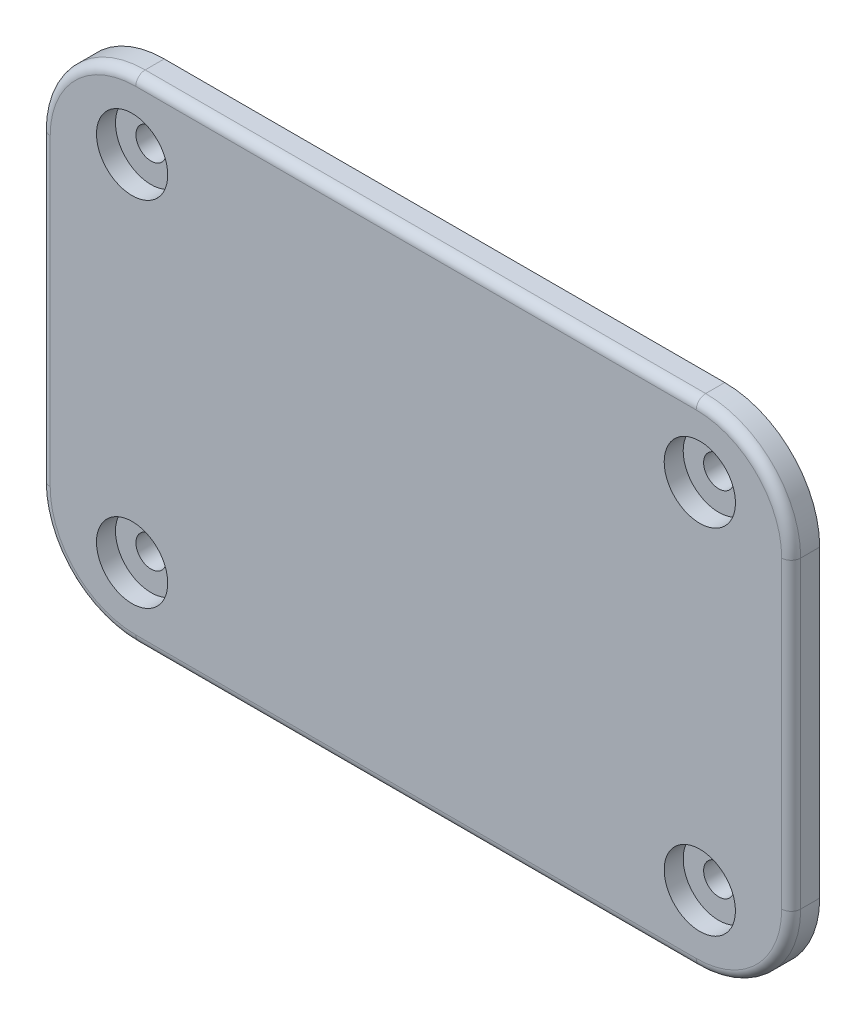
SolidWorks part; units mm, degrees
ref_plane "Ön Düzlem" through (0, 0, 0) normal (0, 0, 1) x (1, 0, 0)
ref_plane "Üst Düzlem" through (0, 0, 0) normal (0, 1, 0) x (1, 0, 0)
ref_plane "Sağ Düzlem" through (0, 0, 0) normal (1, 0, 0) x (0, 0, -1)
sketch "Çizim1" plane through (0, 0, 0) normal (0, 0, 1) x (1, 0, 0)
  line L1 (-29.5, -26) -> (29.5, -26)
  line L2 (-39.5, -16) -> (-39.5, 16)
  line L3 (-29.5, 26) -> (29.5, 26)
  line L4 (39.5, -16) -> (39.5, 16)
  line L5 (-39.5, -26) -> (39.5, 26) construction
  line L6 (-39.5, 26) -> (39.5, -26) construction
  arc A0 (29.5, -26) -> (39.5, -16) centre (29.5, -16) ccw
  arc A1 (-39.5, 16) -> (-29.5, 26) centre (-29.5, 16) cw
  arc A2 (-29.5, -26) -> (-39.5, -16) centre (-29.5, -16) cw
  arc A3 (29.5, 26) -> (39.5, 16) centre (29.5, 16) cw
  point P0 (0, 0)
  dimension "D3" = 10
  dimension "D1" = 79
  dimension "D2" = 52
extrude "Yükseklik-Ekstrüzyon1" add sketch "Çizim1" along normal blind 3
sketch "Çizim4" plane through (0, 0, 0) normal (0, 0, -1) x (-1, 0, 0)
  line L36 (-35.35, 16) -> (-35.35, -16)
  line L37 (29.5, 21.85) -> (-29.5, 21.85)
  line L38 (35.35, -16) -> (35.35, 16)
  line L39 (-29.5, -21.85) -> (29.5, -21.85)
  line L40 (-35.35, 16) -> (-35.35, -16)
  line L41 (29.5, 21.85) -> (-29.5, 21.85)
  line L42 (35.35, -16) -> (35.35, 16)
  line L43 (-29.5, -21.85) -> (29.5, -21.85)
  arc A41 (-35.35, -16) -> (-29.5, -21.85) centre (-29.5, -16) ccw
  arc A42 (-29.5, 21.85) -> (-35.35, 16) centre (-29.5, 16) ccw
  arc A43 (35.35, 16) -> (29.5, 21.85) centre (29.5, 16) ccw
  arc A44 (29.5, -21.85) -> (35.35, -16) centre (29.5, -16) ccw
  arc A45 (-35.35, -16) -> (-29.5, -21.85) centre (-29.5, -16) ccw
  arc A46 (-29.5, 21.85) -> (-35.35, 16) centre (-29.5, 16) ccw
  arc A47 (35.35, 16) -> (29.5, 21.85) centre (29.5, 16) ccw
  arc A48 (29.5, -21.85) -> (35.35, -16) centre (29.5, -16) ccw
  dimension "D1" = 4.15
extrude "Yükseklik-Ekstrüzyon2" add sketch "Çizim4" along normal blind 1.5
fillet "Radyus1" radius 1 8 edges at (0, -26, 3) (-36.5711, -23.0711, 3) (-39.5, 0, 3) (-36.5711, 23.0711, 3) (0, 26, 3) (36.5711, 23.0711, 3) (39.5, 0, 3) (36.5711, -23.0711, 3)
sketch "Çizim5" plane through (0, 0, 3) normal (0, 0, 1) x (1, 0, 0)
  line L0 (30.6791, -15.9455) -> (29.0796, -21.2522) construction
  line L1 (27.1815, -19.2329) -> (32.5771, -17.9648) construction
  line L2 (0, 4.9002) -> (0, -5.0322) construction
  line L3 (21.4256, 0) -> (-21.56, 0) construction
  line L4 (-29.0796, -21.2522) -> (-31.7773, -20.6181) construction
  line L5 (-27.1815, -19.2329) -> (-29.0796, -21.2522) construction
  line L6 (-27.9813, -16.5795) -> (-27.1815, -19.2329) construction
  line L25 (31.7773, -20.6181) -> (32.5771, -17.9648) construction
  line L26 (32.5771, -17.9648) -> (30.6791, -15.9455) construction
  line L27 (30.6791, -15.9455) -> (27.9813, -16.5795) construction
  line L28 (27.9813, -16.5795) -> (27.1815, -19.2329) construction
  line L29 (27.1815, -19.2329) -> (29.0796, -21.2522) construction
  line L30 (29.0796, -21.2522) -> (31.7773, -20.6181) construction
  line L55 (-30.6791, -15.9455) -> (-27.9813, -16.5795) construction
  line L56 (-32.5771, -17.9648) -> (-30.6791, -15.9455) construction
  line L57 (-31.7773, -20.6181) -> (-32.5771, -17.9648) construction
  line L58 (-27.1815, -19.2329) -> (-32.5771, -17.9648) construction
  line L59 (-30.6791, -15.9455) -> (-29.0796, -21.2522) construction
  line L60 (-30.6791, 15.9455) -> (-29.0796, 21.2522) construction
  line L61 (-27.1815, 19.2329) -> (-32.5771, 17.9648) construction
  line L62 (-31.7773, 20.6181) -> (-32.5771, 17.9648) construction
  line L63 (-32.5771, 17.9648) -> (-30.6791, 15.9455) construction
  line L64 (-30.6791, 15.9455) -> (-27.9813, 16.5795) construction
  line L65 (29.0796, 21.2522) -> (31.7773, 20.6181) construction
  line L66 (27.1815, 19.2329) -> (29.0796, 21.2522) construction
  line L67 (27.9813, 16.5795) -> (27.1815, 19.2329) construction
  line L68 (30.6791, 15.9455) -> (27.9813, 16.5795) construction
  line L69 (32.5771, 17.9648) -> (30.6791, 15.9455) construction
  line L70 (31.7773, 20.6181) -> (32.5771, 17.9648) construction
  line L71 (-27.9813, 16.5795) -> (-27.1815, 19.2329) construction
  line L72 (-27.1815, 19.2329) -> (-29.0796, 21.2522) construction
  line L73 (-29.0796, 21.2522) -> (-31.7773, 20.6181) construction
  line L74 (27.1815, 19.2329) -> (32.5771, 17.9648) construction
  line L75 (30.6791, 15.9455) -> (29.0796, 21.2522) construction
  circle A0 centre (29.8793, -18.5988) radius 1.6
  circle A1 centre (-29.8793, -18.5988) radius 1.6
  circle A2 centre (-29.8793, 18.5988) radius 1.6
  circle A3 centre (29.8793, 18.5988) radius 1.6
extrude "Kes-Ekstrüzyon1" cut sketch "Çizim5" against normal blind 5
sketch "Çizim6" plane through (0, 0, 3) normal (0, 0, 1) x (1, 0, 0)
  line L0 (-16.7251, 0) -> (15.2915, 0) construction
  line L1 (0, -7.9643) -> (0, 9.7961) construction
  circle A4 centre (29.8793, -18.5988) radius 3.75
  circle A5 centre (-29.8793, -18.5988) radius 3.75
  circle A6 centre (-29.8793, 18.5988) radius 3.75
  circle A11 centre (29.8793, 18.5988) radius 3.75
  dimension "D1" = 7.5
extrude "Kes-Ekstrüzyon2" cut sketch "Çizim6" against normal blind 2
